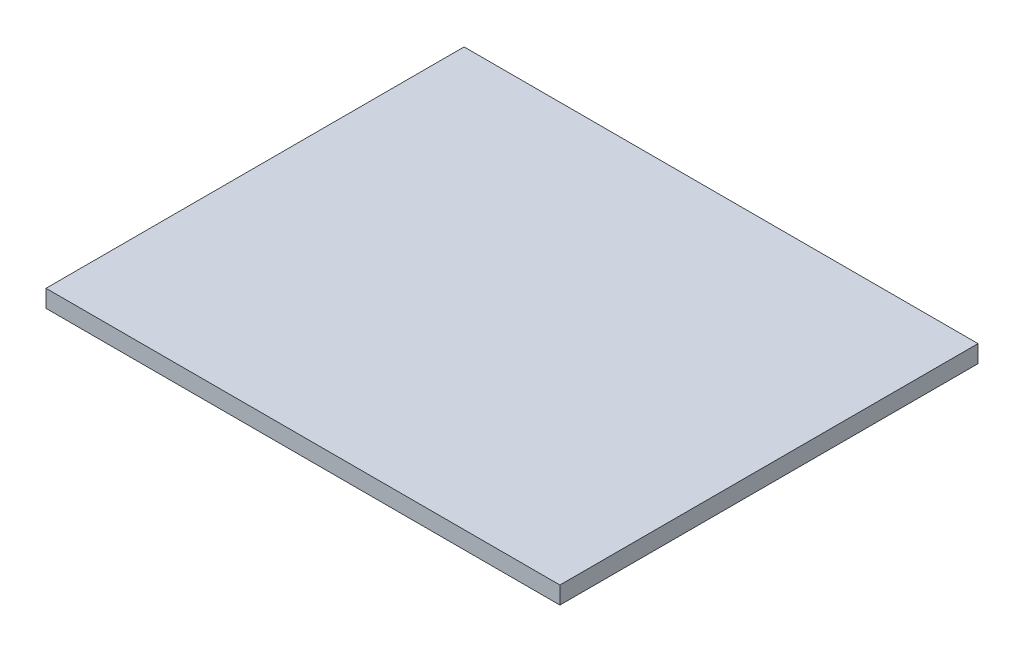
SolidWorks part; units mm, degrees
ref_plane "Front Plane" through (0, 0, 0) normal (0, 0, 1) x (1, 0, 0)
ref_plane "Top Plane" through (0, 0, 0) normal (0, 1, 0) x (1, 0, 0)
ref_plane "Right Plane" through (0, 0, 0) normal (1, 0, 0) x (0, 0, -1)
sketch "Sketch1" plane through (0, 0, 0) normal (0, 1, 0) x (1, 0, 0)
  line L1 (-59, -48) -> (59, -48)
  line L2 (-59, -48) -> (-59, 48)
  line L3 (-59, 48) -> (59, 48)
  line L4 (59, -48) -> (59, 48)
  line L5 (-59, -48) -> (59, 48) construction
  line L6 (-59, 48) -> (59, -48) construction
  point P0 (0, 0)
  dimension "D1" = 118
  dimension "D2" = 96
extrude "Boss-Extrude1" add sketch "Sketch1" along normal blind 4
